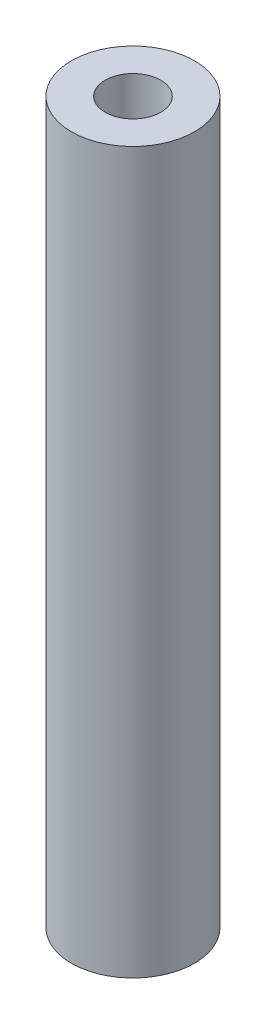
SolidWorks part; units mm, degrees
ref_plane "Front Plane" through (0, 0, 0) normal (0, 0, 1) x (1, 0, 0)
ref_plane "Top Plane" through (0, 0, 0) normal (0, 1, 0) x (1, 0, 0)
ref_plane "Right Plane" through (0, 0, 0) normal (1, 0, 0) x (0, 0, -1)
sketch "Sketch1" plane through (0, 0, 0) normal (0, 1, 0) x (1, 0, 0)
  circle A0 centre (0, 0) radius 4.7625
  circle A1 centre (0, 0) radius 2.1527
  dimension "D1" = 9.525
  dimension "D2" = 4.3053
extrude "Boss-Extrude1" add sketch "Sketch1" along normal blind 55.7276
